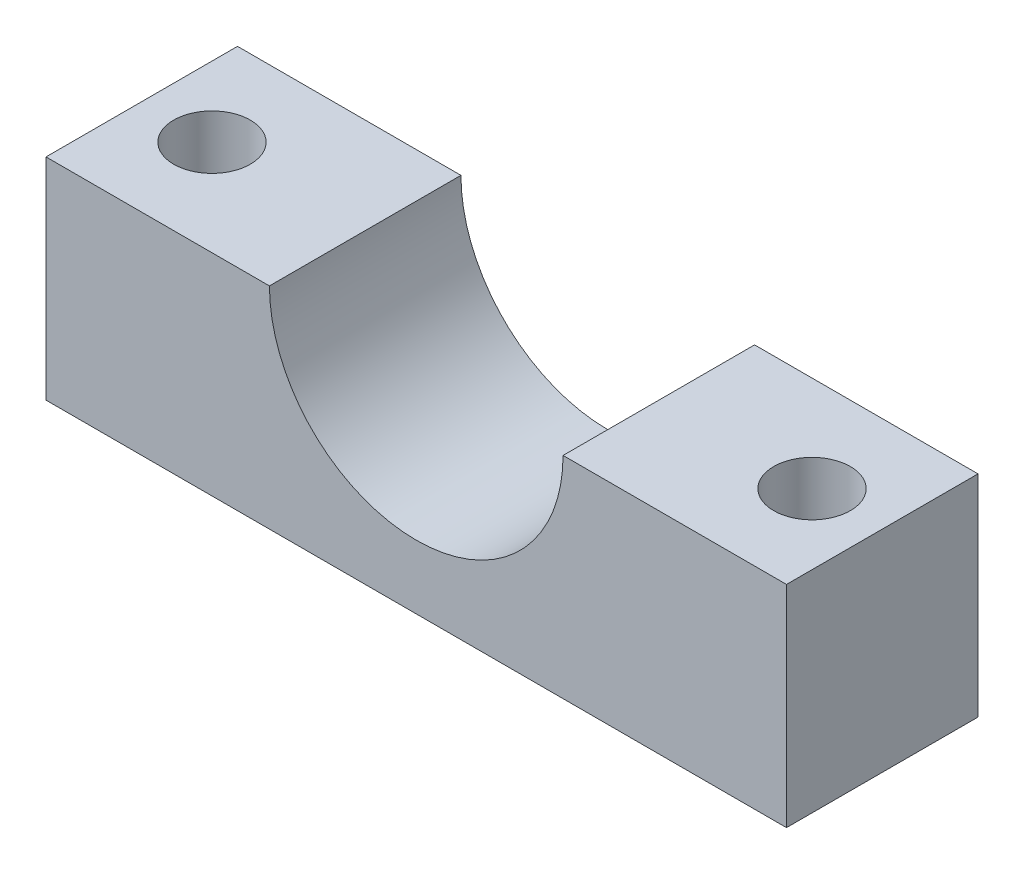
SolidWorks part; units mm, degrees
ref_plane "Płaszczyzna przednia" through (0, 0, 0) normal (0, 0, 1) x (1, 0, 0)
ref_plane "Płaszczyzna górna" through (0, 0, 0) normal (0, 1, 0) x (1, 0, 0)
ref_plane "Płaszczyzna prawa" through (0, 0, 0) normal (1, 0, 0) x (0, 0, -1)
sketch "Szkic1" plane through (0, 0, 0) normal (0, 0, 1) x (1, 0, 0)
  line L0 (-11.5, 0) -> (-29, 0)
  line L1 (-29, 0) -> (-29, -16.5)
  line L2 (-29, -16.5) -> (29, -16.5)
  line L3 (29, -16.5) -> (29, 0)
  line L4 (29, 0) -> (11.5, 0)
  arc A0 (-11.5, 0) -> (11.5, 0) centre (0, 0) ccw
  dimension "D1" = 23
  dimension "D2" = 17.5
  dimension "D3" = 17.5
  dimension "D4" = 16.5
extrude "Dodanie-wyciągnięcie1" add sketch "Szkic1" along normal blind 15
hole_wizard "Otwory ustalające Ø6.0mm1" positions "Szkic2" profile "Szkic3" hole size "Ø6.0" standard "ISO"
sketch "Szkic2" plane through (0, 0, 0) normal (0, 1, 0) x (1, 0, 0)
  line L0 (-29, -15) -> (-29, 0) construction
  line L1 (-11.5, 0) -> (-29, 0) construction
  point P0 (-23.5, -7.5)
  dimension "D1" = 5.5
  dimension "D2" = 7.5
sketch "Szkic3" plane through (-23.5, 0, 7.5) normal (1, 0, 0) x (0, 0, 1)
  line L0 (0, 0) -> (0, 11.8026)
  line L1 (0, 11.8026) -> (3, 10)
  line L2 (3, 10) -> (3, 0)
  line L5 (3, 0) -> (0, 0)
  line L10 (0, 11.8026) -> (-3, 10) construction
  line L11 (0, -6.35) -> (0, 107.95) construction
  dimension "Średnica otworu" = 6
  dimension "Głębokość otworu" = 10
  dimension "Kąt wiertła" = 118
mirror "Lustro1" about plane through (0, 0, 0) normal (1, 0, 0) of "Otwory ustalające Ø6.0mm1"
